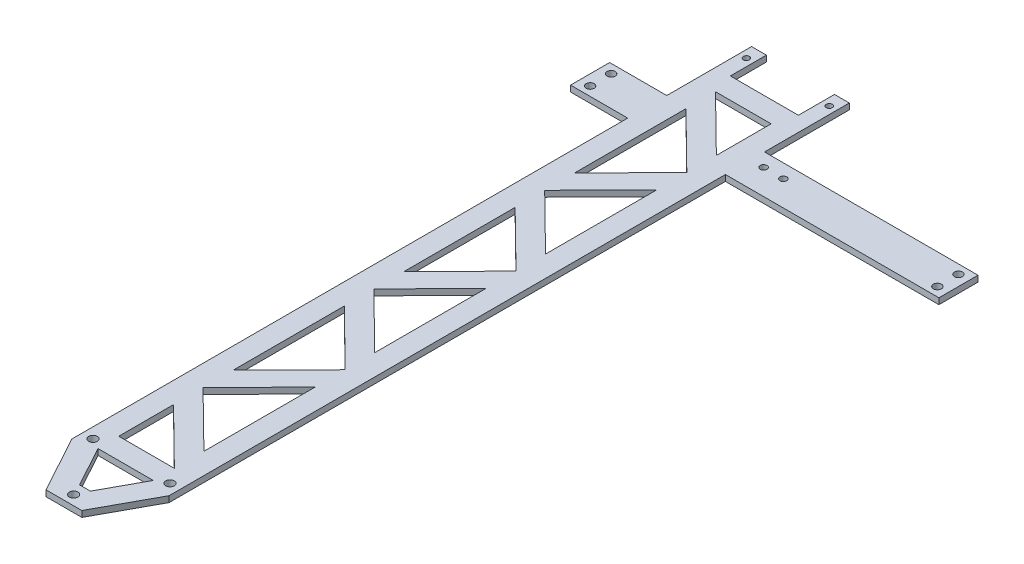
SolidWorks part; units mm, degrees
ref_plane "Front Plane" through (0, 0, 0) normal (0, 0, 1) x (1, 0, 0)
ref_plane "Top Plane" through (0, 0, 0) normal (0, 1, 0) x (1, 0, 0)
ref_plane "Right Plane" through (0, 0, 0) normal (1, 0, 0) x (0, 0, -1)
sketch "Sketch1" plane through (0, 0, 0) normal (0, 1, 0) x (1, 0, 0)
  line L0 (-10.3328, 8.2542) -> (8.1672, 27.048)
  line L1 (-10.2256, -36.7574) -> (8.1372, -36.7574)
  line L2 (-17.3328, -38.3469) -> (-17.3328, 117.6977)
  line L3 (10.2372, 187.6921) -> (15.1672, 187.6921)
  line L4 (15.1672, -38.4867) -> (15.1672, 146.4921)
  line L5 (-10.3328, -29.7574) -> (-10.3328, -11.5466)
  line L6 (-10.3328, -11.5466) -> (8.1672, -29.7574)
  line L7 (-10.3328, -1.7242) -> (8.1672, -19.935)
  line L8 (8.1672, 17.0696) -> (8.1672, -19.935)
  line L9 (-10.3328, -29.7574) -> (8.1672, -29.7574)
  line L10 (-17.3328, 187.6921) -> (-12.4028, 187.6921)
  line L11 (-12.4028, 187.6921) -> (-12.4028, 175.6921)
  line L12 (-10.3328, 65.0596) -> (8.1672, 83.8535)
  line L13 (-10.3328, -1.7242) -> (8.1672, 17.0696)
  line L14 (-10.3328, 8.2542) -> (-10.3328, 45.2588)
  line L15 (-10.3328, 45.2588) -> (8.1672, 27.048)
  line L16 (-10.3328, 55.0812) -> (8.1672, 36.8705)
  line L17 (8.1672, 73.8751) -> (8.1672, 36.8705)
  line L18 (-10.3328, 55.0812) -> (8.1672, 73.8751)
  line L19 (-10.3328, 65.0596) -> (-10.3328, 102.0642)
  line L20 (-10.3328, 102.0642) -> (8.1672, 83.8535)
  line L21 (8.1372, -36.7574) -> (0.7618, -50.2841)
  line L22 (-10.3328, -1.7242) -> (8.1672, 17.0696)
  line L23 (-10.3328, 168.6921) -> (8.1672, 168.6921)
  line L24 (-10.3328, 168.6921) -> (8.1672, 150.4813)
  line L25 (8.1672, 168.6921) -> (8.1672, 150.4813)
  line L26 (-12.4028, 175.6921) -> (10.2372, 175.6921)
  line L27 (10.2372, 187.6921) -> (10.2372, 175.6921)
  line L28 (67.1672, 175.6921) -> (67.1672, 140.6589) construction
  line L29 (-17.3328, 117.6977) -> (-17.3328, 146.4921)
  line L30 (15.1672, 159.4921) -> (15.1672, 187.6921)
  line L31 (86.1672, 152.9921) -> (74.4687, 152.9921) construction
  line L32 (34.1672, 175.6921) -> (34.1672, 140.6589) construction
  line L33 (-6.997, -57.2841) -> (4.918, -57.2841)
  line L34 (-6.997, -57.2841) -> (4.918, -57.2841)
  line L35 (4.918, -57.2841) -> (15.1672, -38.4867)
  line L36 (-6.997, -57.2841) -> (-17.3328, -38.3469)
  line L37 (-10.2256, -36.7574) -> (-2.8428, -50.2841)
  line L38 (-10.3617, 121.8357) -> (8.1672, 140.6589)
  line L39 (-2.8428, -50.2841) -> (0.7618, -50.2841)
  line L40 (-10.3328, 111.8866) -> (8.1672, 93.6759)
  line L41 (8.1672, 130.6805) -> (8.1672, 93.6759)
  line L42 (-10.3328, 111.8866) -> (8.1672, 130.6805)
  line L43 (-10.3617, 121.8357) -> (-10.3617, 158.8981)
  line L44 (-10.3617, 158.8981) -> (8.1672, 140.6589)
  line L45 (15.1672, 159.4921) -> (86.1672, 159.4921)
  line L46 (15.1672, 146.4921) -> (86.1672, 146.4921)
  line L47 (86.1672, 146.4921) -> (86.1672, 159.4921)
  line L48 (-17.3328, 159.4921) -> (-36.3328, 159.4921)
  line L49 (-36.3328, 159.4921) -> (-36.3328, 146.4921)
  line L50 (-36.3328, 146.4921) -> (-17.3328, 146.4921)
  line L51 (-17.3328, 159.4921) -> (-17.3328, 187.6921)
  line L52 (-36.3328, 152.9921) -> (-17.3328, 152.9921) construction
  circle A0 centre (11.7572, -34.7997) radius 1.44
  circle A1 centre (-13.8428, -34.7997) radius 1.44
  circle A2 centre (-1.0428, -54.0597) radius 1.44
  circle A3 centre (-14.8678, 183.496) radius 1
  circle A4 centre (12.7022, 183.496) radius 1
  circle A5 centre (19.4672, 154.8921) radius 1.125
  circle A6 centre (26.0312, 154.8921) radius 1.125
  circle A7 centre (82.6672, 156.4921) radius 1.35
  circle A8 centre (82.6672, 149.4921) radius 1.35
  circle A9 centre (-32.8328, 156.4921) radius 1.35
  circle A10 centre (-32.8328, 149.4921) radius 1.35
  dimension "D5" = 7
  dimension "D12" = 4.3
  dimension "D37" = 2.88
  dimension "D38" = 2.88
  dimension "D39" = 2.88
  dimension "D48" = 2.25
  dimension "D54" = 2.25
  dimension "D55" = 2.7
  dimension "D60" = 2.7
  dimension "D3" = 7
  dimension "D4" = 4.93
  dimension "D6" = 7
  dimension "D7" = 7
  dimension "D8" = 7
  dimension "D9" = 7
  dimension "D10" = 90
  dimension "D11" = 12
  dimension "D13" = 7
  dimension "D14" = 7
  dimension "D15" = 90
  dimension "D16" = 7
  dimension "D17" = 7
  dimension "D18" = 7
  dimension "D19" = 7
  dimension "D20" = 7
  dimension "D21" = 7
  dimension "D22" = 7
  dimension "D23" = 7
  dimension "D24" = 7
  dimension "D25" = 7
  dimension "D26" = 7
  dimension "D27" = 7
  dimension "D28" = 7
  dimension "D29" = 7
  dimension "D30" = 7
  dimension "D31" = 7
  dimension "D32" = 7
  dimension "D33" = 7
  dimension "D34" = 25.6
  dimension "D35" = 3.49
  dimension "D36" = 19.26
  dimension "D40" = 3.7756
  dimension "D41" = 1.9577
  dimension "D42" = 3.6172
  dimension "D43" = 3.62
  dimension "D44" = 1.8046
  dimension "D45" = 1.8
  dimension "D46" = 12.8
  dimension "D47" = 12.8
  dimension "D49" = 33
  dimension "D50" = 4.6
  dimension "D51" = 6.564
  dimension "D52" = 16.2
  dimension "D53" = 13
  dimension "D56" = 3.5
  dimension "D57" = 3.5
  dimension "D58" = 3.5
  dimension "D59" = 3.5
extrude "Boss-Extrude1" add sketch "Sketch1" along normal blind 2
